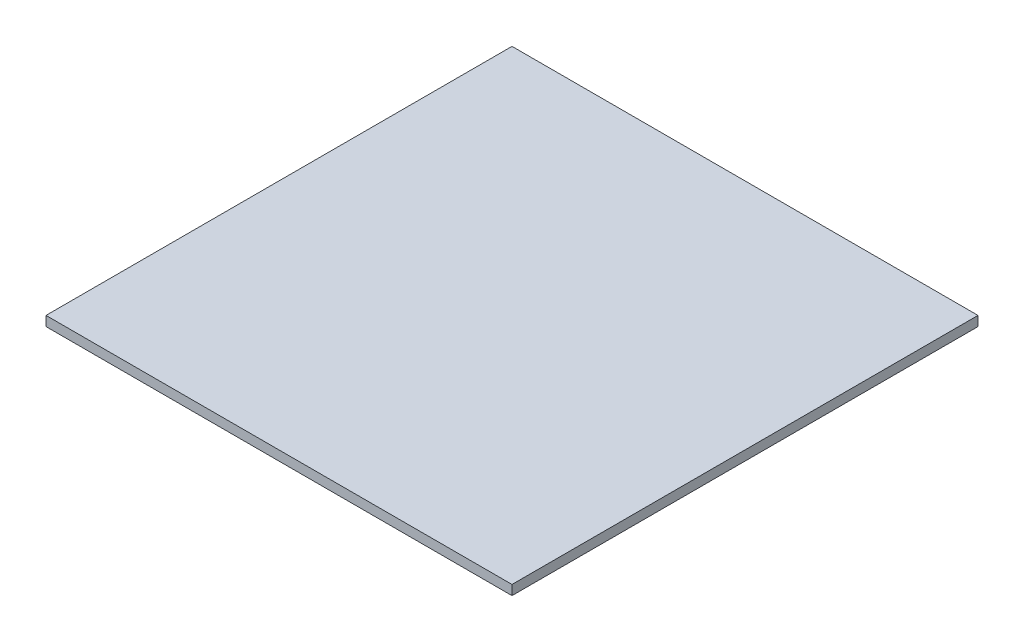
SolidWorks part; units mm, degrees
material "PBT General Purpose"
ref_plane "Front Plane" through (0, 0, 0) normal (0, 0, 1) x (1, 0, 0)
ref_plane "Top Plane" through (0, 0, 0) normal (0, 1, 0) x (1, 0, 0)
ref_plane "Right Plane" through (0, 0, 0) normal (1, 0, 0) x (0, 0, -1)
sketch "Sketch1" plane through (0, 0, 0) normal (0, 1, 0) x (1, 0, 0)
  line L1 (-152.4, -152.4) -> (152.4, -152.4)
  line L2 (-152.4, -152.4) -> (-152.4, 152.4)
  line L3 (-152.4, 152.4) -> (152.4, 152.4)
  line L4 (152.4, -152.4) -> (152.4, 152.4)
  line L5 (-152.4, -152.4) -> (152.4, 152.4) construction
  line L6 (-152.4, 152.4) -> (152.4, -152.4) construction
  point P0 (0, 0)
  dimension "D1" = 304.8
  dimension "D2" = 304.8
extrude "Boss-Extrude1" add sketch "Sketch1" along normal mid plane 6.35
